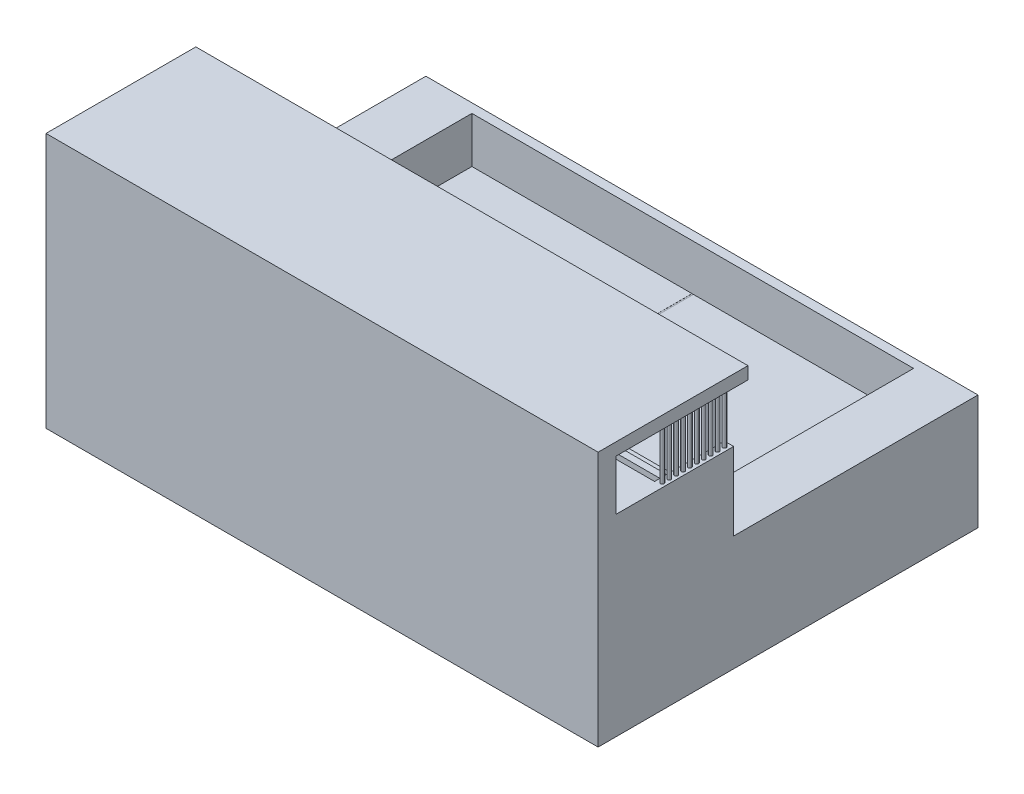
SolidWorks part; units mm, degrees
ref_plane "前基準面" through (0, 0, 0) normal (0, 0, 1) x (1, 0, 0)
ref_plane "上基準面" through (0, 0, 0) normal (0, 1, 0) x (1, 0, 0)
ref_plane "右基準面" through (0, 0, 0) normal (1, 0, 0) x (0, 0, -1)
sketch "草圖1" plane through (0, 0, 0) normal (1, 0, 0) x (0, 0, -1)
  line L1 (-50, 25) -> (50, 25)
  line L2 (-50, 25) -> (-50, -25)
  line L3 (-50, -25) -> (50, -25)
  line L4 (50, 25) -> (50, -25)
  line L5 (-50, 25) -> (50, -25) construction
  line L6 (-50, -25) -> (50, 25) construction
  point P0 (0, 0)
  dimension "D1" = 100
  dimension "D2" = 50
extrude "填料-伸長1" add sketch "草圖1" along normal blind 200
sketch "草圖2" plane through (0, 25, 0) normal (0, 1, 0) x (1, 0, 0)
  line L0 (4, -46) -> (196, -46)
  line L1 (196, -46) -> (196, 46)
  line L2 (196, 46) -> (4, 46)
  line L3 (4, 46) -> (4, -46)
  line L4 (0, 50) -> (0, -50)
  line L5 (0, -50) -> (200, -50)
  line L6 (200, -50) -> (200, 50)
  line L7 (200, 50) -> (0, 50)
  line L8 (0, 50) -> (0, -50)
  line L9 (0, -50) -> (200, -50)
  line L10 (200, -50) -> (200, 50)
  line L11 (200, 50) -> (0, 50)
  dimension "D1" = 0
  dimension "D2" = 4
extrude "除料-伸長1" cut sketch "草圖2" against normal blind 20 contours L0 L1 L2 L3
sketch "草圖3" plane through (0, 0, 0) normal (-1, 0, 0) x (0, 0, 1)
  line L4 (-50, 25) -> (-50, -25)
  line L5 (-50, -25) -> (50, -25)
  line L6 (50, -25) -> (50, 25)
  line L7 (50, 25) -> (-50, 25)
  line L8 (-50, 25) -> (-50, -25)
  line L9 (-50, -25) -> (50, -25)
  line L10 (50, -25) -> (50, 25)
  line L11 (50, 25) -> (-50, 25)
  dimension "D1" = 0
extrude "填料-伸長2" add sketch "草圖3" along normal blind 20
sketch "草圖4" plane through (200, 0, 0) normal (1, 0, 0) x (0, 0, -1)
  line L4 (50, -25) -> (50, 25)
  line L5 (50, 25) -> (-50, 25)
  line L6 (-50, 25) -> (-50, -25)
  line L7 (-50, -25) -> (50, -25)
  line L8 (50, -25) -> (50, 25)
  line L9 (50, 25) -> (-50, 25)
  line L10 (-50, 25) -> (-50, -25)
  line L11 (-50, -25) -> (50, -25)
  dimension "D1" = 0
extrude "填料-伸長3" add sketch "草圖4" along normal blind 20
sketch "草圖6" plane through (4, 0, 0) normal (1, 0, 0) x (0, 0, -1)
  line L0 (0, 0) -> (0, -14.0813) construction
  line L1 (-11.5, 5) -> (11.5, 5)
  line L2 (-11.5, 5) -> (-11.5, 15)
  line L3 (-11.5, 15) -> (11.5, 15)
  line L4 (46, 25) -> (-46, 25)
  line L5 (-46, 25) -> (-46, 5)
  line L6 (-46, 5) -> (46, 5)
  line L7 (46, 5) -> (46, 25)
  line L8 (46, 25) -> (-46, 25)
  line L9 (-46, 25) -> (-46, 5)
  line L10 (-46, 5) -> (46, 5)
  line L11 (46, 5) -> (46, 25)
  line L12 (11.5, 5) -> (11.5, 15)
  line M12 (-46, 5) -> (46, 5)
  dimension "D2" = 23
  dimension "D3" = 10
  dimension "D1" = 0
extrude "除料-伸長2" cut sketch "草圖6" against normal blind 15 contours L12 L3 L2 M12
sketch "草圖7" plane through (196, 0, 0) normal (-1, 0, 0) x (0, 0, 1)
  line L4 (-11.5, 5) -> (11.5, 5)
  line L5 (-11.5, 15) -> (-11.5, 5)
  line L6 (11.5, 15) -> (-11.5, 15)
  line L7 (11.5, 5) -> (11.5, 15)
  line L8 (-11.5, 5) -> (11.5, 5)
  line L9 (-11.5, 15) -> (-11.5, 5)
  line L10 (11.5, 15) -> (-11.5, 15)
  line L11 (11.5, 5) -> (11.5, 15)
  dimension "D1" = 0
extrude "除料-伸長3" cut sketch "草圖7" against normal blind 15
sketch "草圖10" plane through (0, 5, 0) normal (0, 1, 0) x (1, 0, 0)
  line L0 (4, 0) -> (196, 0)
  line L1 (4, 46) -> (4, -46) construction
  line L2 (196, -46) -> (196, 46) construction
  line L3 (100, -46) -> (100, 46)
  line L6 (220, 50) -> (-20, 50)
  line L7 (-20, 50) -> (-20, -50)
  line L8 (-20, -50) -> (220, -50)
  line L9 (220, -50) -> (220, 50)
  line L10 (220, 50) -> (-20, 50)
  line L11 (-20, 50) -> (-20, -50)
  line L12 (-20, -50) -> (220, -50)
  line L13 (220, -50) -> (220, 50)
  circle A0 centre (100, 0) radius 21.3431
  point P13 (100, -46)
  point P16 (100, 43.6244)
  point P17 (100, 52.833)
  point P18 (100, 46)
  dimension "D2" = 96
  dimension "D1" = 0
extrude "除料-伸長-薄件2" cut sketch "草圖10" against normal blind 0.05 thin contours A0 | L3
sketch "草圖11" plane through (220, 0, 0) normal (1, 0, 0) x (0, 0, -1)
  line L0 (-50, 25) -> (-56.2233, 25)
  line L1 (-56.2233, 25) -> (-56.2233, 33.6111)
  line L2 (-56.2233, 33.6111) -> (-59.1455, 33.6111)
  line L3 (-59.1455, 33.6111) -> (-59.1455, 27.1824)
  line L4 (-59.1455, 27.1824) -> (-64.7949, 27.1824)
  line L5 (-64.7949, 27.1824) -> (-64.7949, 32.0526)
  line L6 (-64.7949, 32.0526) -> (-70.0548, 32.0526)
  line L7 (-70.0548, 32.0526) -> (-70.0548, 38.4813)
  line L8 (-70.0548, 38.4813) -> (-76.4835, 38.4813)
  line L9 (-76.4835, 38.4813) -> (-76.4835, 44.5204)
  line L10 (-76.4835, 44.5204) -> (-81.9381, 44.5204)
  line L11 (-81.9381, 44.5204) -> (-81.9381, 50.9491)
  line L12 (-81.9381, 50.9491) -> (-86.6135, 50.9491)
  line L13 (-86.6135, 50.9491) -> (-86.6135, 58.7414)
  line L14 (-86.6135, 58.7414) -> (-107.4581, 58.7414)
  line L15 (-107.4581, 58.7414) -> (-107.4581, 80.6465)
  line L16 (-107.4581, 80.6465) -> (-50, 80.6465)
  line L17 (-50, 80.6465) -> (-50, 86.0326)
  line L18 (-50, 86.0326) -> (-115.1382, 86.0326)
  line L19 (-115.1382, 86.0326) -> (-115.1382, -25)
  line L20 (-115.1382, -25) -> (-50, -25)
  line L21 (-50, 25) -> (-50, -25)
  point P17 (-50, -23.8993)
extrude "填料-伸長4" add sketch "草圖11" against normal up to surface (240 mm away) up to face at (-20, 0, 0)
sketch "草圖12" plane through (220, 0, 0) normal (1, 0, 0) x (0, 0, -1)
  line L0 (-86.6135, 58.7414) -> (-56.2233, 58.7414)
  line L1 (-56.2233, 58.7414) -> (-56.2233, 25)
  line L2 (-86.6135, 58.7414) -> (-86.6135, 25)
  line L3 (-86.6135, 25) -> (-56.2233, 25)
extrude "填料-伸長5" add sketch "草圖12" against normal blind 4
sketch "草圖13" plane through (-20, 0, 0) normal (-1, 0, 0) x (0, 0, 1)
  line L4 (86.6135, 58.7414) -> (56.2233, 58.7414)
  line L5 (56.2233, 58.7414) -> (56.2233, 25)
  line L6 (56.2233, 25) -> (86.6135, 25)
  line L7 (86.6135, 25) -> (86.6135, 58.7414)
  line L8 (86.6135, 58.7414) -> (56.2233, 58.7414)
  line L9 (56.2233, 58.7414) -> (56.2233, 25)
  line L10 (56.2233, 25) -> (86.6135, 25)
  line L11 (86.6135, 25) -> (86.6135, 58.7414)
  dimension "D1" = 0
extrude "填料-伸長6" add sketch "草圖13" against normal blind 4
sketch "草圖14" plane through (0, 86.0326, 0) normal (0, 1, 0) x (1, 0, 0)
  line L0 (99.7, -66.3642) -> (99.7, -126.8129) construction
  line L8 (216, -86.6135) -> (-16, -86.6135)
  line L9 (-16, -86.6135) -> (-16, -56.2233)
  line L10 (-16, -56.2233) -> (-20, -56.2233)
  line L11 (-20, -56.2233) -> (-20, -107.4581)
  line L12 (-20, -107.4581) -> (220, -107.4581)
  line L13 (220, -107.4581) -> (220, -56.2233)
  line L14 (220, -56.2233) -> (216, -56.2233)
  line L15 (216, -56.2233) -> (216, -86.6135)
  line L16 (216, -86.6135) -> (-16, -86.6135)
  line L17 (-16, -86.6135) -> (-16, -56.2233)
  line L18 (-16, -56.2233) -> (-20, -56.2233)
  line L19 (-20, -56.2233) -> (-20, -107.4581)
  line L20 (-20, -107.4581) -> (220, -107.4581)
  line L21 (220, -107.4581) -> (220, -56.2233)
  line L22 (220, -56.2233) -> (216, -56.2233)
  line L23 (216, -56.2233) -> (216, -86.6135)
  circle A0 centre (218.1612, -58.375) radius 0.75
  circle A1 centre (218.1612, -67.375) radius 0.75
  circle A2 centre (218.1612, -70.375) radius 0.75
  circle A3 centre (218.1612, -73.375) radius 0.75
  circle A4 centre (218.1612, -76.375) radius 0.75
  circle A5 centre (218.1612, -79.375) radius 0.75
  circle A6 centre (218.1612, -82.375) radius 0.75
  circle A7 centre (218.1612, -85.375) radius 0.75
  circle A8 centre (218.1612, -64.375) radius 0.75
  circle A9 centre (218.1612, -61.375) radius 0.75
  circle A10 centre (-18.7612, -58.375) radius 0.75
  circle A11 centre (-18.7612, -61.375) radius 0.75
  circle A12 centre (-18.7612, -64.375) radius 0.75
  circle A13 centre (-18.7612, -67.375) radius 0.75
  circle A14 centre (-18.7612, -70.375) radius 0.75
  circle A15 centre (-18.7612, -73.375) radius 0.75
  circle A16 centre (-18.7612, -76.375) radius 0.75
  circle A17 centre (-18.7612, -79.375) radius 0.75
  circle A18 centre (-18.7612, -85.375) radius 0.75
  circle A19 centre (-18.7612, -82.375) radius 0.75
  point P50 (0, 0)
  dimension "D3" = 1.5
  dimension "D2" = 3
  dimension "D4" = 3
  dimension "D5" = 3
  dimension "D6" = 3
  dimension "D7" = 3
  dimension "D8" = 3
  dimension "D9" = 3
  dimension "D10" = 3
  dimension "D11" = 3
  dimension "D1" = 0
extrude "填料-伸長7" add sketch "草圖14" against normal up to surface (27.2912 mm away) contours A4 | A3 | A2 | A1 | A8 | A9 | A0 | A18 | A17 | A14 | A7 | A6 | A5 | A19 | A16 | A15 | A13 | A12 up to face at (100, 58.7414, 76.6296)
